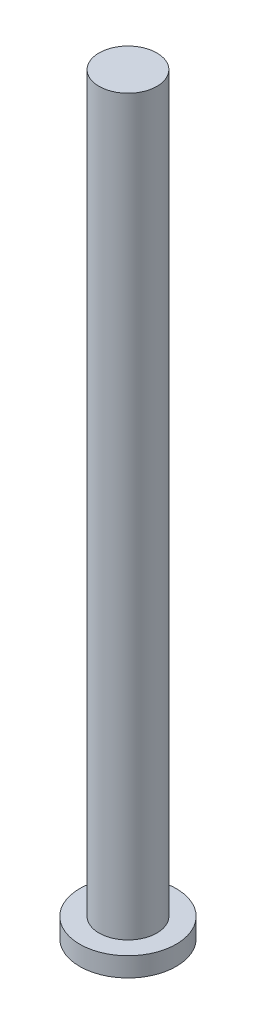
SolidWorks part; units mm, degrees
ref_plane "Front Plane" through (0, 0, 0) normal (0, 0, 1) x (1, 0, 0)
ref_plane "Top Plane" through (0, 0, 0) normal (0, 1, 0) x (1, 0, 0)
ref_plane "Right Plane" through (0, 0, 0) normal (1, 0, 0) x (0, 0, -1)
sketch "Sketch1" plane through (0, 0, 0) normal (0, 1, 0) x (1, 0, 0)
  circle A0 centre (0, 0) radius 2.5
  dimension "D1" = 5
extrude "Boss-Extrude1" add sketch "Sketch1" along normal blind 1
sketch "Sketch2" plane through (0, 1, 0) normal (0, 1, 0) x (1, 0, 0)
  circle A0 centre (0, 0) radius 1.5
  dimension "D1" = 3
extrude "Boss-Extrude2" add sketch "Sketch2" along normal blind 38
